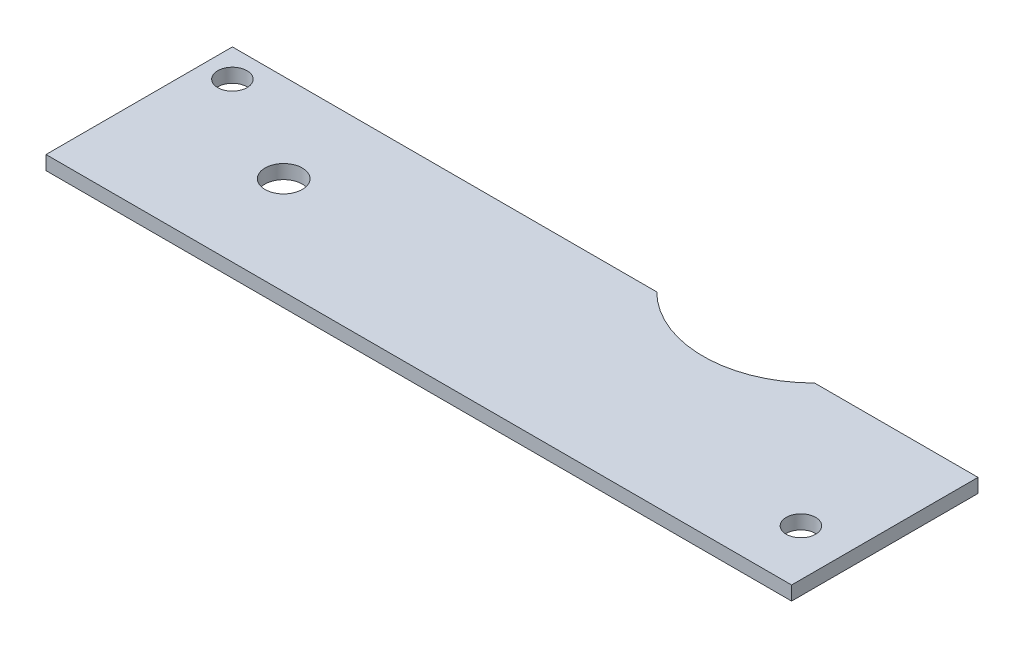
SolidWorks part; units mm, degrees
material "PBT Общее назначение"
ref_plane "Спереди" through (0, 0, 0) normal (0, 0, 1) x (1, 0, 0)
ref_plane "Сверху" through (0, 0, 0) normal (0, 1, 0) x (1, 0, 0)
ref_plane "Справа" through (0, 0, 0) normal (1, 0, 0) x (0, 0, -1)
sketch "Эскиз1" plane through (0, 0, 0) normal (0, 1, 0) x (1, 0, 0)
  line L0 (0, 0) -> (0, 13)
  line L1 (0, 0) -> (80, 0)
  line L2 (0, 13) -> (10.3655, 18.7928)
  line L3 (15, 20) -> (45.5295, 20)
  line L4 (80, 0) -> (80, 20)
  line L5 (62.4705, 20) -> (80, 20)
  line L6 (54, 16.5) -> (80, 16.5) construction
  line L7 (45.5295, 20) -> (62.4705, 20)
  line L8 (15, 20) -> (0, 20)
  line L10 (0, 20) -> (0, 13)
  circle A0 centre (15, 10.5) radius 2
  arc A1 (10.3655, 18.7928) -> (15, 20) centre (15, 10.5) cw
  arc A2 (62.4705, 20) -> (45.5295, 20) centre (54, 28.5) cw
  dimension "D2" = 15
  dimension "D3" = 10.5
  dimension "D5" = 12
  dimension "D7" = 39
  dimension "D9" = 4
  dimension "D1" = 20
  dimension "D4" = 80
  dimension "D6" = 3.5
  dimension "D8" = 13
extrude "Бобышка-Вытянуть1" add sketch "Эскиз1" along normal blind 1.5 contours A1 L2 L0 L1 L4 L5 L7 L3 A0 | L2 A1 L8 L10 | A2 L6 L4 L5
hole_wizard "Под_М3" positions "Эскиз3" profile "Эскиз2" hole size "M3x0.5" standard "DIN"
sketch "Эскиз3" plane through (0, 0, 0) normal (0, -1, 0) x (1, 0, 0)
  circle A0 centre (15, -10.5) radius 2 construction
  point P0 (75, -6)
  point P4 (3, -17)
  dimension "D1" = 60
  dimension "D2" = 4.5
  dimension "D3" = 12
  dimension "D4" = 6.5
sketch "Эскиз2" plane through (75, 0, -6) normal (1, 0, 0) x (0, 0, -1)
  line L0 (0, 0) -> (0, 12.9464)
  line L1 (0, 12.9464) -> (1.575, 12)
  line L2 (1.575, 12) -> (1.575, 0)
  line L5 (1.575, 0) -> (0, 0)
  line L10 (0, 12.9464) -> (-1.575, 12) construction
  line L11 (0, -6.35) -> (0, 107.95) construction
  dimension "Диаметр отверстия" = 3.15
  dimension "Глубина отверстия" = 12
  dimension "Угол заточки сверла" = 118
